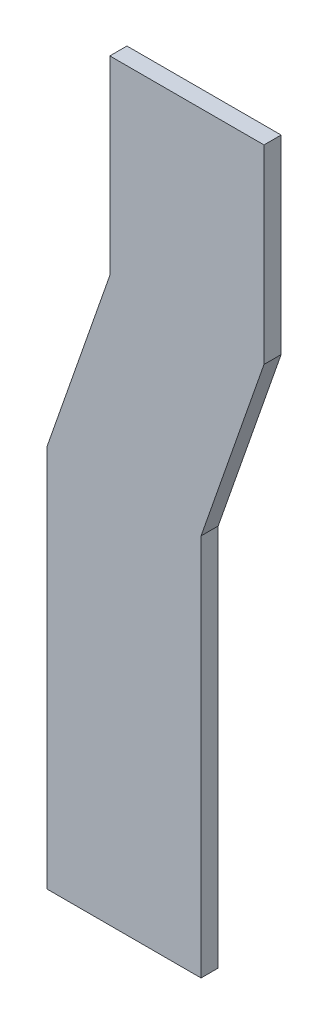
SolidWorks part; units mm, degrees
ref_plane "Front" through (0, 0, 0) normal (0, 0, 1) x (1, 0, 0)
ref_plane "Top" through (0, 0, 0) normal (0, 1, 0) x (1, 0, 0)
ref_plane "Right" through (0, 0, 0) normal (1, 0, 0) x (0, 0, -1)
sketch "Sketch1" plane through (0, 0, 0) normal (0, 0, 1) x (1, 0, 0)
  line L0 (0, 0) -> (180, 0)
  line L1 (180, 0) -> (180, -222)
  line L2 (180, -222) -> (106.514, -432.078)
  line L3 (106.514, -432.078) -> (106.514, -879.078)
  line L4 (0, 0) -> (0, -222)
  line L5 (106.514, -879.078) -> (-73.486, -879.078)
  line L6 (0, -222) -> (-73.486, -432.078)
  line L7 (-73.486, -432.078) -> (-73.486, -879.078)
  dimension "D2" = 180
  dimension "D4" = 160.72
  dimension "D5" = 222.56
  dimension "D6" = 447
  dimension "D7" = 180
  dimension "D8" = 160.72
extrude "Boss-Extrude1" add sketch "Sketch1" along normal mid plane 20
